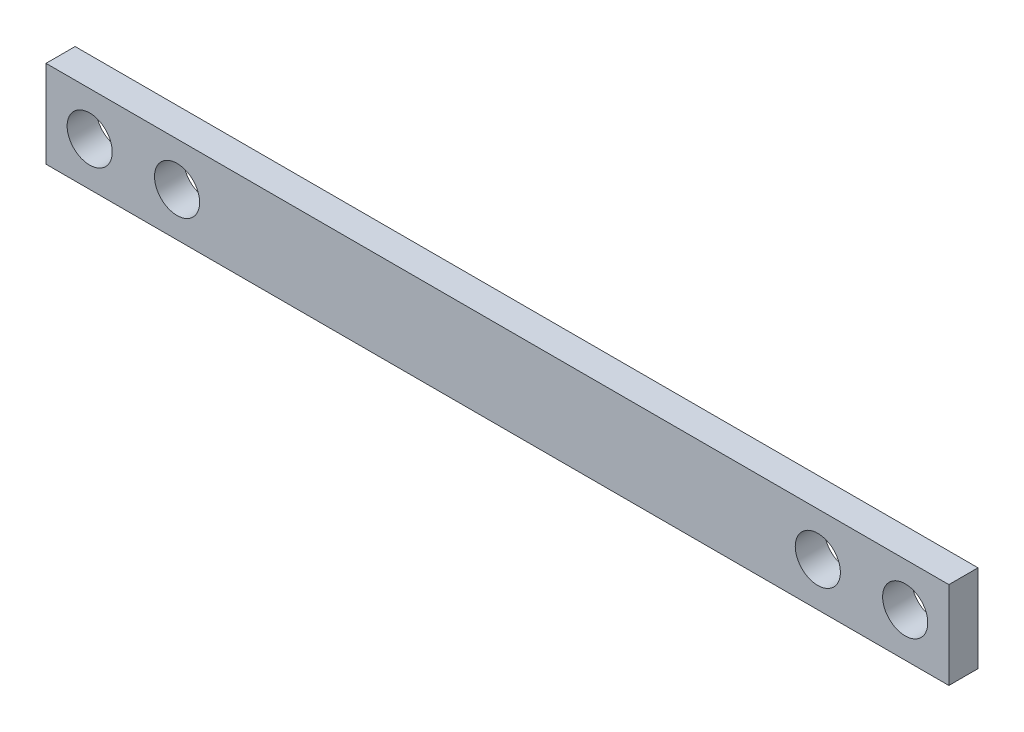
SolidWorks part; units mm, degrees
material "Thornel Mat VMA"
ref_plane "Front Plane" through (0, 0, 0) normal (0, 0, 1) x (1, 0, 0)
ref_plane "Top Plane" through (0, 0, 0) normal (0, 1, 0) x (1, 0, 0)
ref_plane "Right Plane" through (0, 0, 0) normal (1, 0, 0) x (0, 0, -1)
sketch "草图1" plane through (0, 0, 0) normal (0, 0, 1) x (1, 0, 0)
  line L1 (-31, 3) -> (31, 3)
  line L2 (-31, 3) -> (-31, -3)
  line L3 (-31, -3) -> (31, -3)
  line L4 (31, 3) -> (31, -3)
  line L5 (-31, 3) -> (31, -3) construction
  line L6 (-31, -3) -> (31, 3) construction
  point P0 (0, 0)
  dimension "D1" = 6
  dimension "D2" = 62
extrude "凸台-拉伸1" add sketch "草图1" along normal blind 2
sketch "草图2" plane through (0, 0, 2) normal (0, 0, 1) x (1, 0, 0)
  line L0 (-31, 0) -> (31, 0) construction
  line L1 (-31, 3) -> (-31, -3) construction
  line L2 (31, -3) -> (31, 3) construction
  line L3 (0, 0) -> (0, 35.3077) construction
  circle A0 centre (-28, 0) radius 1.55
  circle A1 centre (-22, 0) radius 1.55
  circle A2 centre (22, 0) radius 1.55
  circle A3 centre (28, 0) radius 1.55
  dimension "D1" = 3.1
  dimension "D2" = 3
  dimension "D3" = 6
extrude "切除-拉伸1" cut sketch "草图2" against normal blind 2
